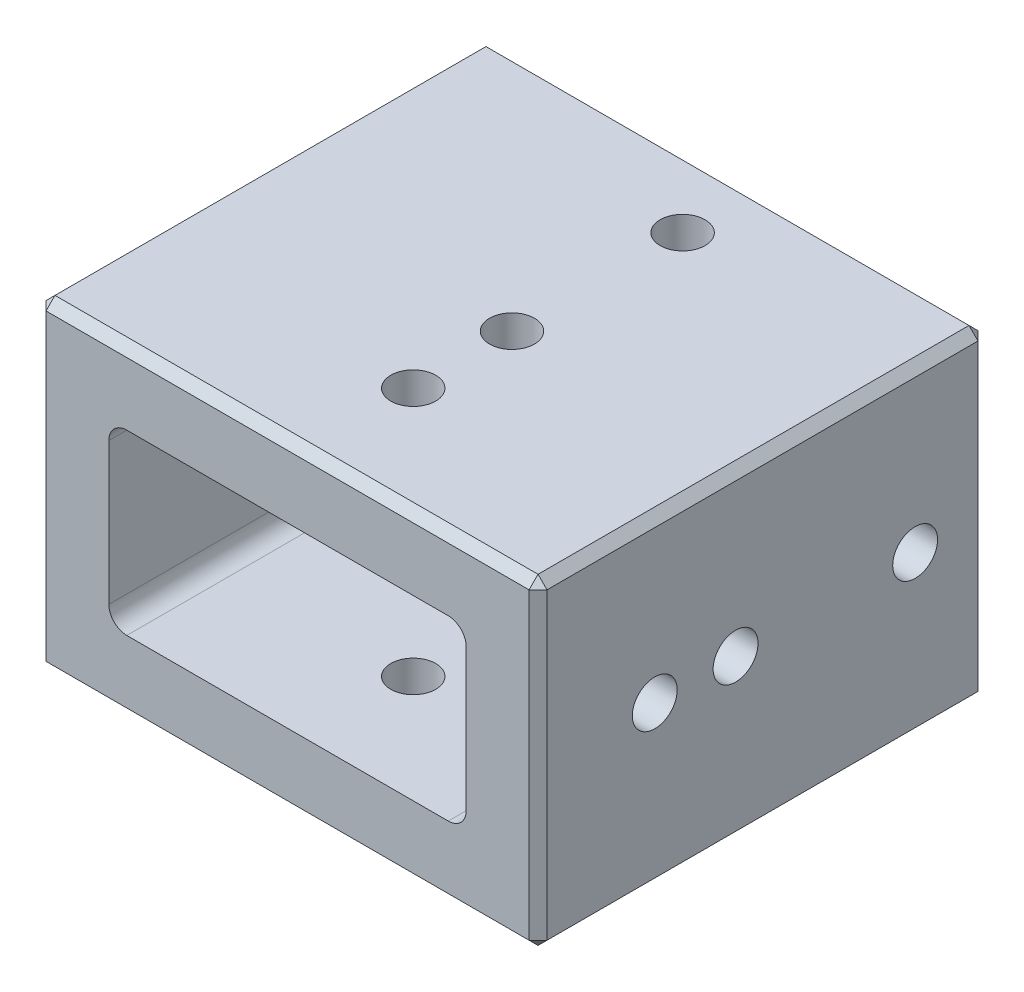
SolidWorks part; units mm, degrees
material "6063-T5"
ref_plane "前视基准面" through (0, 0, 0) normal (0, 0, 1) x (1, 0, 0)
ref_plane "上视基准面" through (0, 0, 0) normal (0, 1, 0) x (1, 0, 0)
ref_plane "右视基准面" through (0, 0, 0) normal (1, 0, 0) x (0, 0, -1)
other "Configuration Table"
sketch "草图2" plane through (0, 0, 0) normal (0, 0, 1) x (1, 0, 0)
  line L1 (-13.95, -8.95) -> (13.95, -8.95)
  line L2 (-13.95, -8.95) -> (-13.95, 8.95)
  line L3 (-13.95, 8.95) -> (13.95, 8.95)
  line L4 (13.95, -8.95) -> (13.95, 8.95)
  line L5 (-13.95, -8.95) -> (13.95, 8.95) construction
  line L6 (-13.95, 8.95) -> (13.95, -8.95) construction
  point P0 (0, 0)
  dimension "D1" = 17.9
  dimension "D2" = 27.9
extrude "凸台-拉伸1" add sketch "草图2" along normal mid plane 25
sketch "草图3" plane through (0, -8.95, 0) normal (0, -1, 0) x (1, 0, 0)
  line L0 (-13.95, -12.5) -> (13.95, -12.5) construction
  line L3 (15, 287.5) -> (15, -12.5) construction
  point P0 (1, -8.5)
  dimension "D1" = 4
  dimension "D2" = 14
hole_wizard "M3 螺纹孔1" positions "3D草图1" profile "草图4" tap size "M3" standard "GB" end condition through all
sketch3d "3D草图1"
  point P0 (1, -8.95, -8.5)
cosmetic thread "孔螺蚊线1" parameters "D2"=3
sketch "草图4" plane through (1, -8.95, -8.5) normal (1, 0, 0) x (0, 0, -1)
  line L0 (0, 0) -> (0, 17.9)
  line L1 (0, 17.9) -> (1.25, 17.9)
  line L2 (1.25, 17.9) -> (1.25, 0)
  line L5 (1.25, 0) -> (0, 0)
  line L11 (0, -6.35) -> (0, 107.95) construction
  dimension "通孔螺纹孔钻头直径" = 2.5
  dimension "通孔螺纹孔钻头深度" = 17.9
sketch "草图5" plane through (-13.95, 0, 0) normal (-1, 0, 0) x (0, 0, 1)
  line L0 (-12.5, 8.95) -> (-12.5, -8.95) construction
  point P0 (-8.5, 0)
  dimension "D1" = 4
hole_wizard "M3 螺纹孔2" positions "3D草图2" profile "草图6" tap size "M3" standard "GB" end condition through all
sketch3d "3D草图2"
  point P0 (-13.95, 0, -8.5)
cosmetic thread "孔螺蚊线2" parameters "D2"=3
sketch "草图6" plane through (-13.95, 0, -8.5) normal (0, 1, 0) x (0, 0, 1)
  line L0 (0, 0) -> (0, 27.9)
  line L1 (0, 27.9) -> (1.25, 27.9)
  line L2 (1.25, 27.9) -> (1.25, 0)
  line L5 (1.25, 0) -> (0, 0)
  line L11 (0, -6.35) -> (0, 107.95) construction
  dimension "通孔螺纹孔钻头直径" = 2.5
  dimension "通孔螺纹孔钻头深度" = 27.9
sketch "草图7" plane through (0, -8.95, 0) normal (0, -1, 0) x (1, 0, 0)
  line L1 (-13.95, 12.5) -> (13.95, 12.5) construction
  line L2 (-13.95, 12.5) -> (-13.95, -12.5) construction
  circle A0 centre (1, 6.5) radius 1.525
  dimension "D1" = 3.05
  dimension "D3" = 14.95
  dimension "D2" = 6
hole_wizard "M3 螺纹孔3" positions "3D草图3" profile "草图8" tap size "M3" standard "GB" end condition through all
sketch3d "3D草图3"
  point P0 (1, -8.95, 6.5)
sketch "草图8" plane through (1, -8.95, 6.5) normal (1, 0, 0) x (0, 0, -1)
  line L0 (0, 0) -> (0, 17.9)
  line L1 (0, 17.9) -> (1.25, 17.9)
  line L2 (1.25, 17.9) -> (1.25, 0)
  line L5 (1.25, 0) -> (0, 0)
  line L11 (0, -6.35) -> (0, 107.95) construction
  dimension "通孔螺纹孔钻头直径" = 2.5
  dimension "通孔螺纹孔钻头深度" = 17.9
cosmetic thread "孔螺蚊线5" parameters "D2"=3
sketch "草图9" plane through (0, 0, -12.5) normal (0, 0, -1) x (-1, 0, 0)
  line L8 (-9.95, 4.95) -> (-9.95, -4.95)
  line L9 (-9.95, -4.95) -> (9.95, -4.95)
  line L10 (9.95, -4.95) -> (9.95, 4.95)
  line L11 (9.95, 4.95) -> (-9.95, 4.95)
  line L12 (-9.95, 4.95) -> (-9.95, -4.95)
  line L13 (-9.95, -4.95) -> (9.95, -4.95)
  line L14 (9.95, -4.95) -> (9.95, 4.95)
  line L15 (9.95, 4.95) -> (-9.95, 4.95)
  dimension "D1" = 4
extrude "切除-拉伸1" cut sketch "草图9" against normal through all
chamfer "倒角2" distance 0.5 angle 45 12 edges at (-13.95, 0, 12.5) (0, 8.95, 12.5) (13.95, 0, 12.5) (0, -8.95, 12.5) (0, -8.95, -12.5) (13.95, -8.95, 0) (-13.95, -8.95, 0) (-13.95, 0, -12.5) (-13.95, 8.95, 0) (0, 8.95, -12.5) (13.95, 0, -12.5) (13.95, 8.95, 0)
sketch "草图10" plane through (13.95, 0, 0) normal (1, 0, 0) x (0, 0, -1)
  line L0 (12.5, 8.45) -> (12.5, -8.45) construction
  circle A0 centre (-1.5, 0) radius 1.525
  dimension "D1" = 3.05
  dimension "D2" = 14
hole_wizard "M3 螺纹孔4" positions "3D草图4" profile "草图11" tap size "M3" standard "GB" end condition through all
sketch3d "3D草图4"
  point P0 (13.95, 0, 1.5)
sketch "草图11" plane through (13.95, 0, 1.5) normal (0, 1, 0) x (0, 0, -1)
  line L0 (0, 0) -> (0, 27.9)
  line L1 (0, 27.9) -> (1.25, 27.9)
  line L2 (1.25, 27.9) -> (1.25, 0)
  line L5 (1.25, 0) -> (0, 0)
  line L11 (0, -6.35) -> (0, 107.95) construction
  dimension "通孔螺纹孔钻头直径" = 2.5
  dimension "通孔螺纹孔钻头深度" = 27.9
cosmetic thread "孔螺蚊线6" parameters "D2"=3
sketch "草图15" plane through (13.95, 0, 0) normal (1, 0, 0) x (0, 0, -1)
  line L0 (-12.5, -8.45) -> (-12.5, 8.45) construction
  line L1 (-12, 8.95) -> (12, 8.95) construction
  point P0 (-6, 0)
  dimension "D1" = 6.5
  dimension "D2" = 8.95
hole_wizard "M3 螺纹孔6" positions "3D草图7" profile "草图16" tap size "M3" standard "GB" end condition up to next
sketch3d "3D草图7"
  point P0 (13.95, 0, 6)
sketch "草图16" plane through (13.95, 0, 6) normal (0, 1, 0) x (0, 0, -1)
  line L0 (0, 0) -> (0, 4)
  line L1 (0, 4) -> (1.25, 4)
  line L2 (1.25, 4) -> (1.25, 0)
  line L5 (1.25, 0) -> (0, 0)
  line L11 (0, -6.35) -> (0, 107.95) construction
  dimension "通孔螺纹孔钻头直径" = 2.5
  dimension "通孔螺纹孔钻头深度" = 4
cosmetic thread "孔螺蚊线13" parameters "D1"=12, "D2"=3.5
sketch "草图17" plane through (0, 8.95, 0) normal (0, 1, 0) x (1, 0, 0)
  line L0 (13.95, 12) -> (13.95, -12) construction
  line L1 (-13.45, 12.5) -> (13.45, 12.5) construction
  point P0 (1, -1)
  dimension "D1" = 12.95
  dimension "D2" = 13.5
hole_wizard "M3 螺纹孔7" positions "3D草图8" profile "草图18" tap size "M3" standard "GB" end condition through all
sketch3d "3D草图8"
  point P0 (1, 8.95, 1)
sketch "草图18" plane through (1, 8.95, 1) normal (1, 0, 0) x (0, 0, 1)
  line L0 (0, 0) -> (0, 17.9)
  line L1 (0, 17.9) -> (1.25, 17.9)
  line L2 (1.25, 17.9) -> (1.25, 0)
  line L5 (1.25, 0) -> (0, 0)
  line L11 (0, -6.35) -> (0, 107.95) construction
  dimension "通孔螺纹孔钻头直径" = 2.5
  dimension "通孔螺纹孔钻头深度" = 17.9
cosmetic thread "孔螺蚊线14" parameters "D2"=3
fillet "圆角1" radius 1 4 edges at (-9.95, -4.95, 0) (9.95, -4.95, 0) (9.95, 4.95, 0) (-9.95, 4.95, 0)
